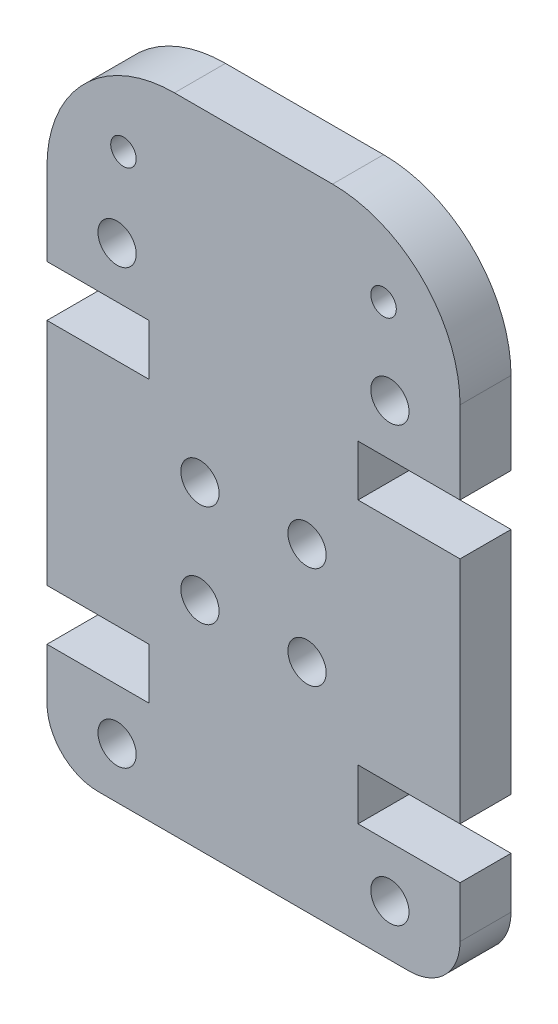
SolidWorks part; units mm, degrees
ref_plane "Front Plane" through (0, 0, 0) normal (0, 0, 1) x (1, 0, 0)
ref_plane "Top Plane" through (0, 0, 0) normal (0, 1, 0) x (1, 0, 0)
ref_plane "Right Plane" through (0, 0, 0) normal (1, 0, 0) x (0, 0, -1)
sketch "Sketch1" plane through (0, 0, 0) normal (0, 0, 1) x (1, 0, 0)
  line L0 (8.1, 25.23) -> (8.1, 0) construction
  line L1 (12.2, 4) -> (16.2, 4)
  line L2 (12.2, 6) -> (12.2, 4)
  line L3 (16.2, 6) -> (12.2, 6)
  line L4 (16.2, 2) -> (16.2, 4)
  line L5 (16.2, 15) -> (12.2, 15)
  line L6 (12.2, 15) -> (12.2, 17)
  line L7 (12.2, 17) -> (16.2, 17)
  line L8 (16.2, 20.23) -> (16.2, 17)
  line L9 (16.2, 6) -> (16.2, 15)
  line L20 (0, 6) -> (0, 15)
  line L22 (0, 20.23) -> (0, 17)
  line L26 (4, 17) -> (0, 17)
  line L27 (4, 15) -> (4, 17)
  line L29 (0, 15) -> (4, 15)
  line L30 (5, 25.23) -> (11.2, 25.23)
  line L31 (2, 0) -> (14.2, 0)
  line L33 (0, 2) -> (0, 4)
  line L34 (0, 6) -> (4, 6)
  line L36 (4, 6) -> (4, 4)
  line L37 (4, 4) -> (0, 4)
  circle A0 centre (13.45, 2) radius 0.75
  arc A1 (16.2, 2) -> (14.2, 0) centre (14.2, 2) cw
  circle A2 centre (13.2, 22.23) radius 0.5
  arc A3 (11.2, 25.23) -> (16.2, 20.23) centre (11.2, 20.23) cw
  circle A4 centre (10.2, 8.5) radius 0.75
  circle A5 centre (13.45, 19) radius 0.75
  circle A6 centre (10.2, 12.5) radius 0.75
  circle A10 centre (6, 12.5) radius 0.75
  circle A12 centre (2.75, 19) radius 0.75
  circle A15 centre (6, 8.5) radius 0.75
  arc A17 (5, 25.23) -> (0, 20.23) centre (5, 20.23) ccw
  circle A19 centre (3, 22.23) radius 0.5
  arc A21 (0, 2) -> (2, 0) centre (2, 2) ccw
  circle A23 centre (2.75, 2) radius 0.75
  dimension "D1" = 1
  dimension "D2" = 1.5
  dimension "D3" = 5
  dimension "D4" = 2
  dimension "D5" = 3
  dimension "D6" = 6
  dimension "D7" = 8.1
  dimension "D8" = 8.5
  dimension "D9" = 2.5
  dimension "D10" = 15
  dimension "D11" = 2
  dimension "D12" = 3
  dimension "D13" = 25.23
extrude "Boss-Extrude1" add sketch "Sketch1" along normal blind 2
equation "\"D7@Sketch1\"= \"fingerWidth@parametersSketch@prostheticParameters.SLDPRT\" / 2 'DIP width"
equation "\"D13@Sketch1\"= \"HL@parametersSketch@prostheticParameters.SLDPRT\" * 0.158 - 4 'DIP length - Sil. Sht DIP"
